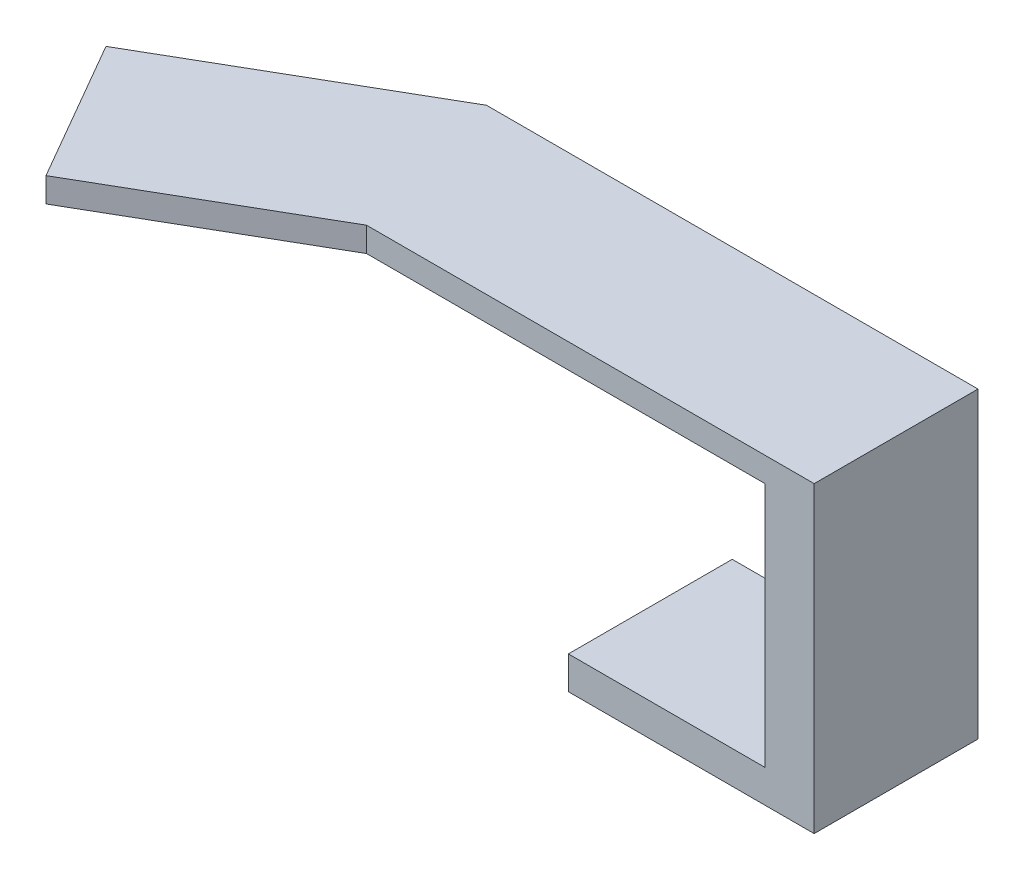
SolidWorks part; units mm, degrees
ref_plane "Front Plane" through (0, 0, 0) normal (0, 0, 1) x (1, 0, 0)
ref_plane "Top Plane" through (0, 0, 0) normal (0, 1, 0) x (1, 0, 0)
ref_plane "Right Plane" through (0, 0, 0) normal (1, 0, 0) x (0, 0, -1)
sketch "Sketch1" plane through (0, 0, 0) normal (0, 1, 0) x (1, 0, 0)
  line L0 (-10.6066, 3.5355) -> (-25.329, -4.9645)
  line L1 (-7.9271, -6.4645) -> (19.3934, -6.4645)
  line L3 (-10.6066, 3.5355) -> (19.3934, 3.5355)
  line L4 (19.3934, -6.4645) -> (19.3934, 3.5355)
  line L5 (-2.6047, -0.4749) -> (19.3934, 3.5355) construction
  line L6 (-10.6066, 3.5355) -> (19.3934, -6.4645) construction
  line L7 (-25.329, -4.9645) -> (-20.329, -13.6247)
  line L8 (-20.329, -13.6247) -> (-7.9271, -6.4645)
  point P0 (0, 0)
  dimension "D1" = 10
  dimension "D2" = 30
  dimension "D3" = 150
  dimension "D4" = 17
  dimension "D5" = 10
extrude "Boss-Extrude1" add sketch "Sketch1" along normal blind 1.5
sketch "Sketch2" plane through (0, 0, 0) normal (0, -1, 0) x (1, 0, 0)
  line L0 (19.3934, -3.5355) -> (-10.6066, -3.5355) construction
  line L1 (19.3934, 6.4645) -> (16.3934, 6.4645)
  line L2 (19.3934, 6.4645) -> (19.3934, -3.5355)
  line L3 (19.3934, -3.5355) -> (16.3934, -3.5355)
  line L4 (16.3934, 6.4645) -> (16.3934, -3.5355)
  dimension "D1" = 3
extrude "Boss-Extrude2" add sketch "Sketch2" along normal blind 17
sketch "Sketch3" plane through (16.3934, 0, 0) normal (-1, 0, 0) x (0, 0, 1)
  line L0 (6.4645, -17) -> (6.4645, 0) construction
  line L1 (-3.5355, -17) -> (6.4645, -17)
  line L2 (-3.5355, -17) -> (-3.5355, -15)
  line L3 (-3.5355, -15) -> (6.4645, -15)
  line L4 (6.4645, -17) -> (6.4645, -15)
  dimension "D1" = 2
extrude "Boss-Extrude3" add sketch "Sketch3" along normal blind 12
